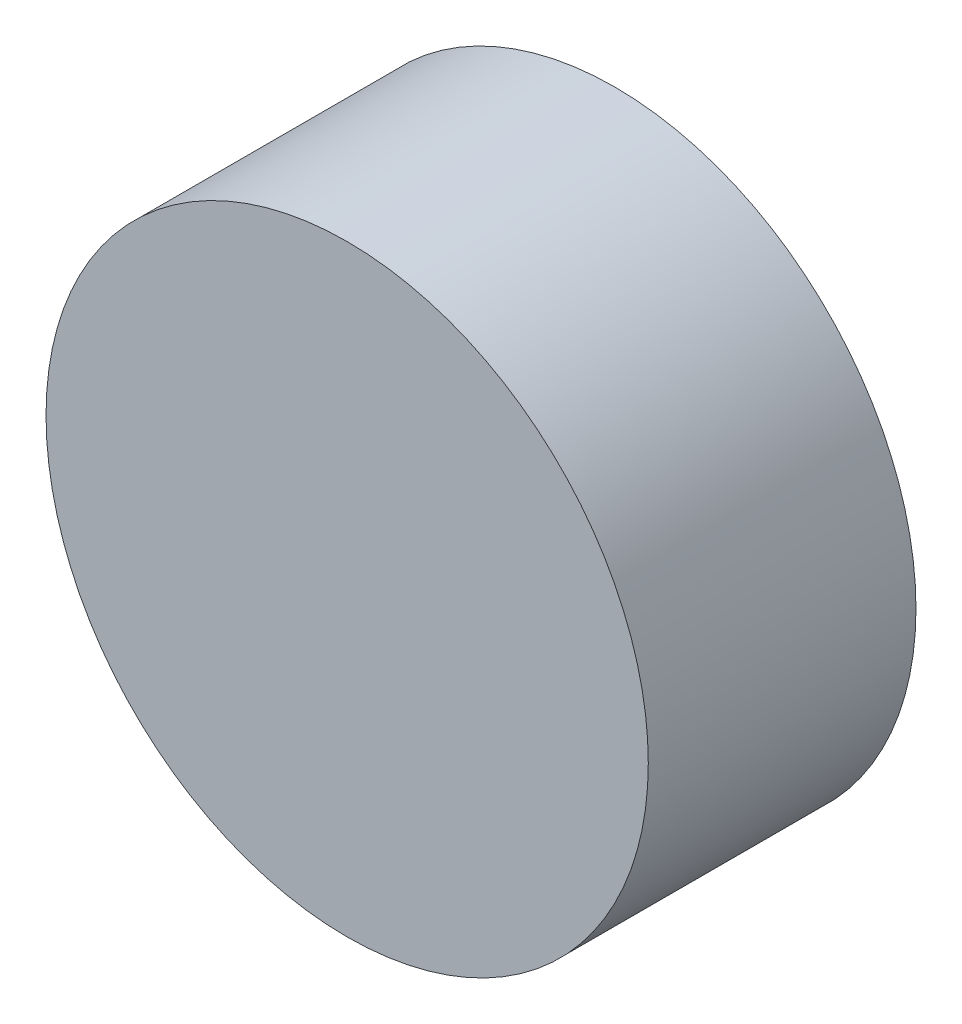
SolidWorks part; units mm, degrees
ref_plane "Front Plane" through (0, 0, 0) normal (0, 0, 1) x (1, 0, 0)
ref_plane "Top Plane" through (0, 0, 0) normal (0, 1, 0) x (1, 0, 0)
ref_plane "Right Plane" through (0, 0, 0) normal (1, 0, 0) x (0, 0, -1)
sketch "Sketch1" plane through (0, 0, 0) normal (0, 0, 1) x (1, 0, 0)
  circle A0 centre (0, 0) radius 4.5
  dimension "D1" = 9
extrude "Boss-Extrude1" add sketch "Sketch1" along normal blind 4 contours A0
sketch "Sketch2" plane through (0, 0, 0) normal (0, 0, -1) x (-1, 0, 0)
  circle A0 centre (0, 0) radius 2.5
  dimension "D1" = 5
extrude "Cut-Extrude1" cut sketch "Sketch2" against normal blind 3
